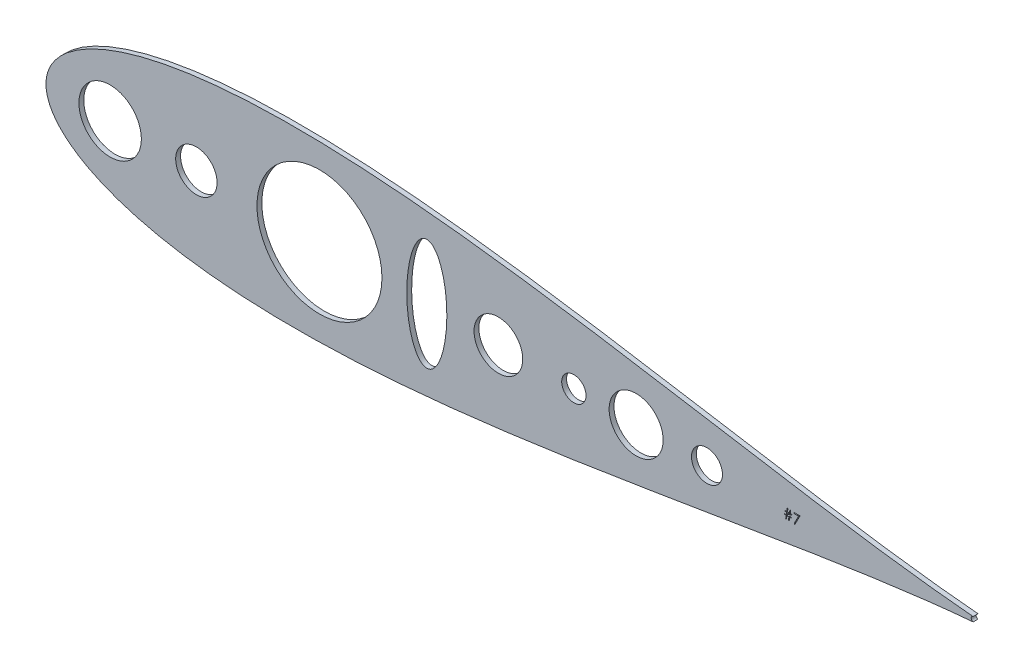
SolidWorks part; units mm, degrees
material "Balsa"
ref_plane "Front Plane" through (0, 0, 0) normal (0, 0, 1) x (1, 0, 0)
ref_plane "Top Plane" through (0, 0, 0) normal (0, 1, 0) x (1, 0, 0)
ref_plane "Right Plane" through (0, 0, 0) normal (1, 0, 0) x (0, 0, -1)
sketch "Sketch2" plane through (0, 0, 0) normal (0, 0, 1) x (1, 0, 0)
  line L0 (310.3693, -1.4598) -> (310.3693, -1.7854)
  line L1 (310.3693, -1.7854) -> (309.3984, -1.7854)
  line L2 (309.3984, -1.7854) -> (309.1349, -3.5439)
  line L3 (309.1349, -3.5439) -> (308.7411, -3.5439)
  line L4 (308.7411, -3.5439) -> (309.0046, -1.7854)
  line L5 (309.0046, -1.7854) -> (307.9656, -1.7854)
  line L6 (307.9656, -1.7854) -> (307.7021, -3.5439)
  line L7 (307.7021, -3.5439) -> (307.3082, -3.5439)
  line L8 (307.3082, -3.5439) -> (307.5718, -1.7854)
  line L9 (307.5718, -1.7854) -> (306.7221, -1.7854)
  line L10 (306.7221, -1.7854) -> (306.7221, -1.4598)
  line L11 (306.7221, -1.4598) -> (307.6206, -1.4598)
  line L12 (307.6206, -1.4598) -> (307.7967, -0.2875)
  line L13 (307.7967, -0.2875) -> (306.8523, -0.2875)
  line L14 (306.8523, -0.2875) -> (306.8523, 0.0382)
  line L15 (306.8523, 0.0382) -> (307.8455, 0.0382)
  line L16 (307.8455, 0.0382) -> (308.0898, 1.6664)
  line L17 (308.0898, 1.6664) -> (308.4826, 1.6664)
  line L18 (308.4826, 1.6664) -> (308.2383, 0.0382)
  line L19 (308.2383, 0.0382) -> (309.2784, 0.0382)
  line L20 (309.2784, 0.0382) -> (309.5226, 1.6664)
  line L21 (309.5226, 1.6664) -> (309.9154, 1.6664)
  line L22 (309.9154, 1.6664) -> (309.6712, 0.0382)
  line L23 (309.6712, 0.0382) -> (310.4995, 0.0382)
  line L24 (310.4995, 0.0382) -> (310.4995, -0.2875)
  line L25 (310.4995, -0.2875) -> (309.6223, -0.2875)
  line L26 (309.6223, -0.2875) -> (309.4473, -1.4598)
  line L27 (309.4473, -1.4598) -> (310.3693, -1.4598)
  line L28 (309.2295, -0.2875) -> (308.1895, -0.2875)
  line L29 (308.1895, -0.2875) -> (308.0145, -1.4598)
  line L30 (308.0145, -1.4598) -> (309.0535, -1.4598)
  line L31 (309.0535, -1.4598) -> (309.2295, -0.2875)
  line L32 (311.6718, 1.5361) -> (314.798, 1.5361)
  line L33 (314.798, 1.5361) -> (312.1277, -3.6741)
  line L34 (312.1277, -3.6741) -> (311.7339, -3.4574)
  line L35 (311.7339, -3.4574) -> (314.0266, 1.0151)
  line L36 (314.0266, 1.0151) -> (311.6718, 1.0151)
  line L37 (311.6718, 1.0151) -> (311.6718, 1.5361)
  circle A0 centre (-44.9758, 0) radius 16.2849
  circle A1 centre (266.2658, 0) radius 8.0865
  circle A2 centre (229.3265, 0) radius 14.0957
  circle A3 centre (196.85, 0) radius 6.35
  circle A4 centre (157.48, 0) radius 12.7
  circle A5 centre (64.1859, 0) radius 32.5896
  circle A6 centre (0, 0) radius 10.795
  arc A7 (405.0574, 1.2193) -> (405.0544, -1.2196) centre (405.3049, -0.0004) ccw
  ellipse E0 centre (120.1709, 0) end of major axis (120.1709, -29.1012) minor radius 10.4447
  spline S0 degree 3 poles (405.0574, 1.2193) (404.7798, 1.2426) (401.9558, 1.4813) (396.2842, 2.0055) (387.7002, 2.8985) (378.1829, 3.9942) (367.7682, 5.2993) (356.5044, 6.8151) (344.4405, 8.5382) (331.6285, 10.4597) (318.123, 12.5659) (303.9805, 14.8379) (289.2595, 17.2525) (274.02, 19.7816) (258.3237, 22.3935) (242.2338, 25.0526) (225.8144, 27.7204) (209.1312, 30.3559) (192.2509, 32.9163) (175.2416, 35.3575) (158.1723, 37.6348) (141.1135, 39.704) (124.1368, 41.5213) (107.315, 43.0449) (90.7221, 44.2351) (74.4334, 45.0551) (58.5255, 45.4718) (43.076, 45.4563) (28.1637, 44.9841) (13.8688, 44.0368) (0.2728, 42.6005) (-12.5412, 40.6687) (-24.4878, 38.2409) (-35.4786, 35.3251) (-45.4206, 31.9385) (-54.2148, 28.1111) (-61.7542, 23.8938) (-67.9263, 19.372) (-72.6271, 14.6934) (-75.8097, 10.1055) (-77.5844, 5.9663) (-78.301, 2.6459) (-78.4642, 0) (-78.301, -2.6459) (-77.5844, -5.9663) (-75.8097, -10.1055) (-72.6271, -14.6934) (-67.9263, -19.372) (-61.7542, -23.8938) (-54.2148, -28.1111) (-45.4206, -31.9385) (-35.4786, -35.3251) (-24.4878, -38.2409) (-12.5412, -40.6687) (0.2728, -42.6005) (13.8688, -44.0368) (28.1637, -44.9841) (43.076, -45.4563) (58.5255, -45.4718) (74.4334, -45.0551) (90.7221, -44.2351) (107.315, -43.0449) (124.1368, -41.5213) (141.1135, -39.704) (158.1723, -37.6348) (175.2416, -35.3575) (192.2509, -32.9163) (209.1312, -30.3559) (225.8144, -27.7204) (242.2338, -25.0526) (258.3237, -22.3935) (274.02, -19.7816) (289.2595, -17.2525) (303.9805, -14.8379) (318.123, -12.5659) (331.6285, -10.4597) (344.4405, -8.5382) (356.5044, -6.8151) (367.7682, -5.2993) (378.1829, -3.9942) (387.7002, -2.8985) (396.2842, -2.0055) (401.9548, -1.4814) (404.7778, -1.2427) (405.0544, -1.2196) knots 0.020477 0.020477 0.020477 0.020477 0.021271 0.028553 0.036781 0.04592 0.055932 0.066773 0.078397 0.090755 0.103793 0.117456 0.131686 0.146422 0.1616 0.177156 0.193024 0.209135 0.225421 0.241812 0.258238 0.274629 0.290914 0.307025 0.322893 0.338448 0.353626 0.368361 0.38259 0.396253 0.40929 0.421647 0.43327 0.444109 0.454119 0.463255 0.471479 0.478755 0.485052 0.490344 0.49461 0.497833 0.5 0.502167 0.50539 0.509656 0.514948 0.521245 0.528521 0.536745 0.545881 0.555891 0.56673 0.578353 0.59071 0.603747 0.61741 0.631639 0.646374 0.661552 0.677107 0.692975 0.709086 0.725371 0.741762 0.758188 0.774579 0.790865 0.806976 0.822844 0.8384 0.853578 0.868314 0.882544 0.896207 0.909245 0.921603 0.933227 0.944068 0.95408 0.963219 0.971447 0.978729 0.97952 0.97952 0.97952 0.97952
  dimension "D1" = 32.5697
  dimension "D2" = 21.59
  dimension "D3" = 65.1792
  dimension "D4" = 25.4
  dimension "D5" = 12.7
  dimension "D6" = 28.1914
  dimension "D7" = 16.1729
  dimension "D8" = 1.2446
  dimension "D10" = 64.1859
  dimension "D53" = 44.9758
extrude "Boss-Extrude1" add sketch "Sketch2" along normal blind 2.54 contours A7 S0 L36 L37 L32 L33 L34 L35 L26 L27 L0 L1 L2 L3 L4 L5 L6 L7 L8 L9 L10 L11 L12 L13 L14 L15 L16 L17 L18 L19 L20 L21 L22 L23 L24 L25 A0 A1 A2 A3 A4 A5
